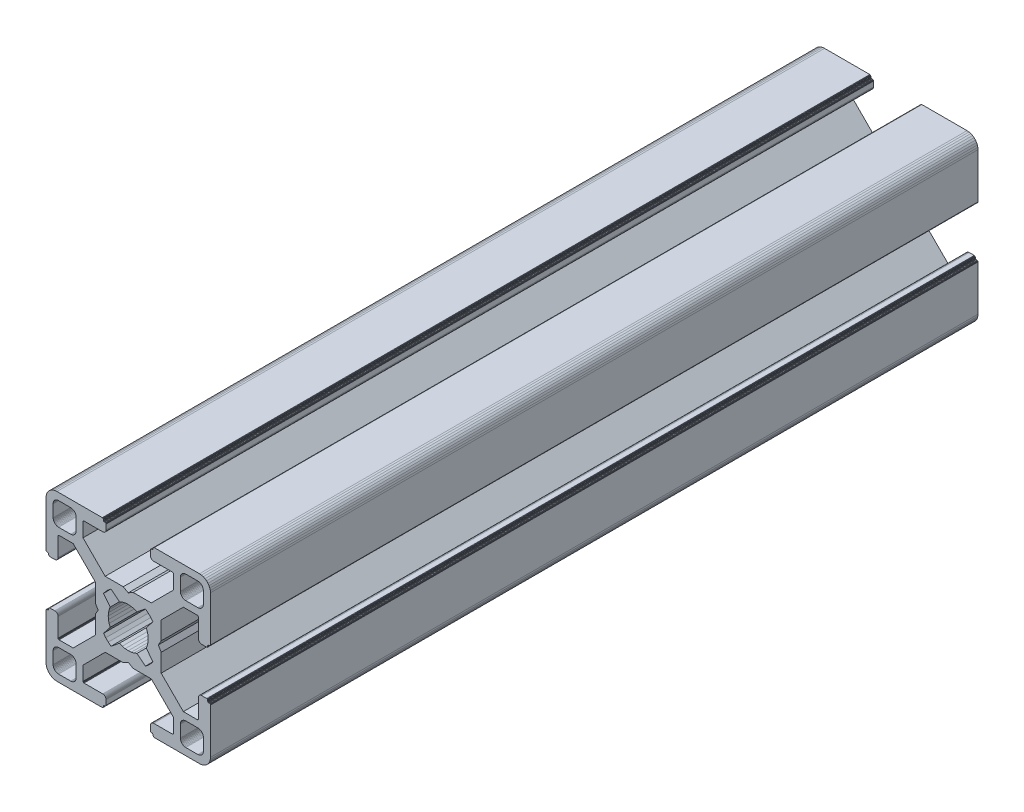
SolidWorks part; units mm, degrees
ref_plane "Front Plane" through (0, 0, 0) normal (0, 0, 1) x (1, 0, 0)
ref_plane "Top Plane" through (0, 0, 0) normal (0, 1, 0) x (1, 0, 0)
ref_plane "Right Plane" through (0, 0, 0) normal (1, 0, 0) x (0, 0, -1)
ref_plane "Plane1" through (0, 0, 0) normal (0, 0, 1) x (1, 0, 0)
sketch "Sketch1" plane through (0, 0, 0) normal (0, 0, 1) x (1, 0, 0)
  line L0 (28.3473, 29.9696) -> (28, 30)
  line L1 (28, 30) -> (19.75, 30)
  line L2 (19.75, 30) -> (19.7153, 29.997)
  line L3 (19.7153, 29.997) -> (19.6816, 29.9879)
  line L4 (19.6816, 29.9879) -> (19.65, 29.9732)
  line L5 (19.65, 29.9732) -> (19.6214, 29.9532)
  line L6 (19.6214, 29.9532) -> (19.5968, 29.9286)
  line L7 (19.5968, 29.9286) -> (19.5768, 29.9)
  line L8 (19.5768, 29.9) -> (19.5621, 29.8684)
  line L9 (19.5621, 29.8684) -> (19.553, 29.8347)
  line L10 (19.553, 29.8347) -> (19.55, 29.8)
  line L11 (19.55, 29.8) -> (19.55, 29.7)
  line L12 (19.55, 29.7) -> (19.547, 29.6653)
  line L13 (19.547, 29.6653) -> (19.5379, 29.6316)
  line L14 (19.5379, 29.6316) -> (19.5232, 29.6)
  line L15 (19.5232, 29.6) -> (19.5032, 29.5714)
  line L16 (19.5032, 29.5714) -> (19.4786, 29.5468)
  line L17 (19.4786, 29.5468) -> (19.45, 29.5268)
  line L18 (19.45, 29.5268) -> (19.4184, 29.5121)
  line L19 (19.4184, 29.5121) -> (19.3847, 29.503)
  line L20 (19.3847, 29.503) -> (19.35, 29.5)
  line L21 (19.35, 29.5) -> (19.25, 29.5)
  line L22 (19.25, 29.5) -> (19.2153, 29.497)
  line L23 (19.2153, 29.497) -> (19.1816, 29.4879)
  line L24 (19.1816, 29.4879) -> (19.15, 29.4732)
  line L25 (19.15, 29.4732) -> (19.1214, 29.4532)
  line L26 (19.1214, 29.4532) -> (19.0968, 29.4286)
  line L27 (19.0968, 29.4286) -> (19.0768, 29.4)
  line L28 (19.0768, 29.4) -> (19.0621, 29.3684)
  line L29 (19.0621, 29.3684) -> (19.053, 29.3347)
  line L30 (19.053, 29.3347) -> (19.05, 29.3)
  line L31 (19.05, 29.3) -> (19.05, 28.4)
  line L32 (19.05, 28.4) -> (19.0591, 28.2958)
  line L33 (19.0591, 28.2958) -> (19.0862, 28.1948)
  line L34 (19.0862, 28.1948) -> (19.1304, 28.1)
  line L35 (19.1304, 28.1) -> (19.1904, 28.0143)
  line L36 (19.1904, 28.0143) -> (19.2643, 27.9404)
  line L37 (19.2643, 27.9404) -> (19.35, 27.8804)
  line L38 (19.35, 27.8804) -> (19.4448, 27.8362)
  line L39 (19.4448, 27.8362) -> (19.5458, 27.8091)
  line L40 (19.5458, 27.8091) -> (19.65, 27.8)
  line L41 (19.65, 27.8) -> (23.05, 27.8)
  line L42 (23.05, 27.8) -> (23.0847, 27.7969)
  line L43 (23.0847, 27.7969) -> (23.1184, 27.7879)
  line L44 (23.1184, 27.7879) -> (23.15, 27.7732)
  line L45 (23.15, 27.7732) -> (23.1786, 27.7532)
  line L46 (23.1786, 27.7532) -> (23.2032, 27.7285)
  line L47 (23.2032, 27.7285) -> (23.2232, 27.7)
  line L48 (23.2232, 27.7) -> (23.2379, 27.6684)
  line L49 (23.2379, 27.6684) -> (23.247, 27.6347)
  line L50 (23.247, 27.6347) -> (23.25, 27.6)
  line L51 (23.25, 27.6) -> (23.25, 25.05)
  line L52 (23.25, 25.05) -> (19.2045, 21)
  line L53 (19.2045, 21) -> (15.9, 21)
  line L54 (15.9, 21) -> (15, 20.4848)
  line L55 (15, 20.4848) -> (14.1, 21)
  line L56 (14.1, 21) -> (10.7955, 21)
  line L57 (10.7955, 21) -> (7.9973, 23.8013)
  line L58 (7.9973, 23.8013) -> (6.75, 25.05)
  line L59 (6.75, 25.05) -> (6.75, 27.6)
  line L60 (6.75, 27.6) -> (6.753, 27.6347)
  line L61 (6.753, 27.6347) -> (6.7621, 27.6684)
  line L62 (6.7621, 27.6684) -> (6.7768, 27.7)
  line L63 (6.7768, 27.7) -> (6.7968, 27.7285)
  line L64 (6.7968, 27.7285) -> (6.8215, 27.7532)
  line L65 (6.8215, 27.7532) -> (6.85, 27.7732)
  line L66 (6.85, 27.7732) -> (6.8816, 27.7879)
  line L67 (6.8816, 27.7879) -> (6.9153, 27.7969)
  line L68 (6.9153, 27.7969) -> (6.95, 27.8)
  line L69 (6.95, 27.8) -> (10.35, 27.8)
  line L70 (10.35, 27.8) -> (10.4542, 27.8091)
  line L71 (10.4542, 27.8091) -> (10.5552, 27.8362)
  line L72 (10.5552, 27.8362) -> (10.65, 27.8804)
  line L73 (10.65, 27.8804) -> (10.7357, 27.9404)
  line L74 (10.7357, 27.9404) -> (10.8096, 28.0143)
  line L75 (10.8096, 28.0143) -> (10.8696, 28.1)
  line L76 (10.8696, 28.1) -> (10.9138, 28.1948)
  line L77 (10.9138, 28.1948) -> (10.9409, 28.2958)
  line L78 (10.9409, 28.2958) -> (10.95, 28.4)
  line L79 (10.95, 28.4) -> (10.95, 29.3)
  line L80 (10.95, 29.3) -> (10.947, 29.3347)
  line L81 (10.947, 29.3347) -> (10.938, 29.3684)
  line L82 (10.938, 29.3684) -> (10.9232, 29.4)
  line L83 (10.9232, 29.4) -> (10.9032, 29.4286)
  line L84 (10.9032, 29.4286) -> (10.8786, 29.4532)
  line L85 (10.8786, 29.4532) -> (10.85, 29.4732)
  line L86 (10.85, 29.4732) -> (10.8184, 29.4879)
  line L87 (10.8184, 29.4879) -> (10.7847, 29.497)
  line L88 (10.7847, 29.497) -> (10.75, 29.5)
  line L89 (10.75, 29.5) -> (10.65, 29.5)
  line L90 (10.65, 29.5) -> (10.6153, 29.503)
  line L91 (10.6153, 29.503) -> (10.5816, 29.5121)
  line L92 (10.5816, 29.5121) -> (10.55, 29.5268)
  line L93 (10.55, 29.5268) -> (10.5214, 29.5468)
  line L94 (10.5214, 29.5468) -> (10.4968, 29.5714)
  line L95 (10.4968, 29.5714) -> (10.4768, 29.6)
  line L96 (10.4768, 29.6) -> (10.4621, 29.6316)
  line L97 (10.4621, 29.6316) -> (10.453, 29.6653)
  line L98 (10.453, 29.6653) -> (10.45, 29.7)
  line L99 (10.45, 29.7) -> (10.45, 29.8)
  line L100 (10.45, 29.8) -> (10.447, 29.8347)
  line L101 (10.447, 29.8347) -> (10.4379, 29.8684)
  line L102 (10.4379, 29.8684) -> (10.4232, 29.9)
  line L103 (10.4232, 29.9) -> (10.4032, 29.9286)
  line L104 (10.4032, 29.9286) -> (10.3786, 29.9532)
  line L105 (10.3786, 29.9532) -> (10.35, 29.9732)
  line L106 (10.35, 29.9732) -> (10.3184, 29.9879)
  line L107 (10.3184, 29.9879) -> (10.2847, 29.997)
  line L108 (10.2847, 29.997) -> (10.25, 30)
  line L109 (10.25, 30) -> (2, 30)
  line L110 (2, 30) -> (1.6527, 29.9696)
  line L111 (1.6527, 29.9696) -> (1.316, 29.8794)
  line L112 (1.316, 29.8794) -> (1, 29.7321)
  line L113 (1, 29.7321) -> (0.7144, 29.5321)
  line L114 (0.7144, 29.5321) -> (0.4679, 29.2856)
  line L115 (0.4679, 29.2856) -> (0.2679, 29)
  line L116 (0.2679, 29) -> (0.1206, 28.684)
  line L117 (0.1206, 28.684) -> (0.0304, 28.3473)
  line L118 (0.0304, 28.3473) -> (0, 28)
  line L119 (0, 28) -> (0, 19.75)
  line L120 (0, 19.75) -> (0.003, 19.7153)
  line L121 (0.003, 19.7153) -> (0.0121, 19.6816)
  line L122 (0.0121, 19.6816) -> (0.0268, 19.65)
  line L123 (0.0268, 19.65) -> (0.0468, 19.6214)
  line L124 (0.0468, 19.6214) -> (0.0714, 19.5968)
  line L125 (0.0714, 19.5968) -> (0.1, 19.5768)
  line L126 (0.1, 19.5768) -> (0.1316, 19.5621)
  line L127 (0.1316, 19.5621) -> (0.1653, 19.553)
  line L128 (0.1653, 19.553) -> (0.2, 19.55)
  line L129 (0.2, 19.55) -> (0.3, 19.55)
  line L130 (0.3, 19.55) -> (0.3347, 19.547)
  line L131 (0.3347, 19.547) -> (0.3684, 19.5379)
  line L132 (0.3684, 19.5379) -> (0.4, 19.5232)
  line L133 (0.4, 19.5232) -> (0.4286, 19.5032)
  line L134 (0.4286, 19.5032) -> (0.4532, 19.4786)
  line L135 (0.4532, 19.4786) -> (0.4732, 19.45)
  line L136 (0.4732, 19.45) -> (0.4879, 19.4184)
  line L137 (0.4879, 19.4184) -> (0.497, 19.3847)
  line L138 (0.497, 19.3847) -> (0.5, 19.35)
  line L139 (0.5, 19.35) -> (0.5, 19.25)
  line L140 (0.5, 19.25) -> (0.503, 19.2153)
  line L141 (0.503, 19.2153) -> (0.5121, 19.1816)
  line L142 (0.5121, 19.1816) -> (0.5268, 19.15)
  line L143 (0.5268, 19.15) -> (0.5468, 19.1214)
  line L144 (0.5468, 19.1214) -> (0.5714, 19.0968)
  line L145 (0.5714, 19.0968) -> (0.6, 19.0768)
  line L146 (0.6, 19.0768) -> (0.6316, 19.0621)
  line L147 (0.6316, 19.0621) -> (0.6653, 19.053)
  line L148 (0.6653, 19.053) -> (0.7, 19.05)
  line L149 (0.7, 19.05) -> (1.6, 19.05)
  line L150 (1.6, 19.05) -> (1.7042, 19.0591)
  line L151 (1.7042, 19.0591) -> (1.8052, 19.0862)
  line L152 (1.8052, 19.0862) -> (1.9, 19.1304)
  line L153 (1.9, 19.1304) -> (1.9857, 19.1904)
  line L154 (1.9857, 19.1904) -> (2.0596, 19.2643)
  line L155 (2.0596, 19.2643) -> (2.1196, 19.35)
  line L156 (2.1196, 19.35) -> (2.1638, 19.4448)
  line L157 (2.1638, 19.4448) -> (2.1909, 19.5458)
  line L158 (2.1909, 19.5458) -> (2.2, 19.65)
  line L159 (2.2, 19.65) -> (2.2, 23.05)
  line L160 (2.2, 23.05) -> (2.203, 23.0847)
  line L161 (2.203, 23.0847) -> (2.2121, 23.1184)
  line L162 (2.2121, 23.1184) -> (2.2268, 23.15)
  line L163 (2.2268, 23.15) -> (2.2468, 23.1786)
  line L164 (2.2468, 23.1786) -> (2.2714, 23.2032)
  line L165 (2.2714, 23.2032) -> (2.3, 23.2232)
  line L166 (2.3, 23.2232) -> (2.3316, 23.2379)
  line L167 (2.3316, 23.2379) -> (2.3653, 23.247)
  line L168 (2.3653, 23.247) -> (2.4, 23.25)
  line L169 (2.4, 23.25) -> (4.95, 23.25)
  line L170 (4.95, 23.25) -> (7.9973, 20.2027)
  line L171 (7.9973, 20.2027) -> (8.9955, 19.2045)
  line L172 (8.9955, 19.2045) -> (8.9955, 15.9)
  line L173 (8.9955, 15.9) -> (9.5151, 15)
  line L174 (9.5151, 15) -> (8.9955, 14.1)
  line L175 (8.9955, 14.1) -> (8.9955, 10.7955)
  line L176 (8.9955, 10.7955) -> (4.95, 6.75)
  line L177 (4.95, 6.75) -> (2.4, 6.75)
  line L178 (2.4, 6.75) -> (2.3653, 6.753)
  line L179 (2.3653, 6.753) -> (2.3316, 6.7621)
  line L180 (2.3316, 6.7621) -> (2.3, 6.7768)
  line L181 (2.3, 6.7768) -> (2.2714, 6.7968)
  line L182 (2.2714, 6.7968) -> (2.2468, 6.8214)
  line L183 (2.2468, 6.8214) -> (2.2268, 6.85)
  line L184 (2.2268, 6.85) -> (2.2121, 6.8816)
  line L185 (2.2121, 6.8816) -> (2.203, 6.9153)
  line L186 (2.203, 6.9153) -> (2.2, 6.95)
  line L187 (2.2, 6.95) -> (2.2, 10.35)
  line L188 (2.2, 10.35) -> (2.1909, 10.4542)
  line L189 (2.1909, 10.4542) -> (2.1638, 10.5552)
  line L190 (2.1638, 10.5552) -> (2.1196, 10.65)
  line L191 (2.1196, 10.65) -> (2.0596, 10.7357)
  line L192 (2.0596, 10.7357) -> (1.9857, 10.8096)
  line L193 (1.9857, 10.8096) -> (1.9, 10.8696)
  line L194 (1.9, 10.8696) -> (1.8052, 10.9138)
  line L195 (1.8052, 10.9138) -> (1.7042, 10.9409)
  line L196 (1.7042, 10.9409) -> (1.6, 10.95)
  line L197 (1.6, 10.95) -> (0.7, 10.95)
  line L198 (0.7, 10.95) -> (0.6653, 10.9469)
  line L199 (0.6653, 10.9469) -> (0.6316, 10.9379)
  line L200 (0.6316, 10.9379) -> (0.6, 10.9232)
  line L201 (0.6, 10.9232) -> (0.5715, 10.9032)
  line L202 (0.5715, 10.9032) -> (0.5468, 10.8785)
  line L203 (0.5468, 10.8785) -> (0.5268, 10.85)
  line L204 (0.5268, 10.85) -> (0.5121, 10.8184)
  line L205 (0.5121, 10.8184) -> (0.503, 10.7847)
  line L206 (0.503, 10.7847) -> (0.5, 10.75)
  line L207 (0.5, 10.75) -> (0.5, 10.65)
  line L208 (0.5, 10.65) -> (0.497, 10.6153)
  line L209 (0.497, 10.6153) -> (0.4879, 10.5816)
  line L210 (0.4879, 10.5816) -> (0.4732, 10.55)
  line L211 (0.4732, 10.55) -> (0.4532, 10.5214)
  line L212 (0.4532, 10.5214) -> (0.4286, 10.4968)
  line L213 (0.4286, 10.4968) -> (0.4, 10.4768)
  line L214 (0.4, 10.4768) -> (0.3684, 10.4621)
  line L215 (0.3684, 10.4621) -> (0.3347, 10.453)
  line L216 (0.3347, 10.453) -> (0.3, 10.45)
  line L217 (0.3, 10.45) -> (0.2, 10.45)
  line L218 (0.2, 10.45) -> (0.1653, 10.447)
  line L219 (0.1653, 10.447) -> (0.1316, 10.4379)
  line L220 (0.1316, 10.4379) -> (0.1, 10.4232)
  line L221 (0.1, 10.4232) -> (0.0714, 10.4032)
  line L222 (0.0714, 10.4032) -> (0.0468, 10.3786)
  line L223 (0.0468, 10.3786) -> (0.0268, 10.35)
  line L224 (0.0268, 10.35) -> (0.0121, 10.3184)
  line L225 (0.0121, 10.3184) -> (0.003, 10.2847)
  line L226 (0.003, 10.2847) -> (0, 10.25)
  line L227 (0, 10.25) -> (0, 2)
  line L228 (0, 2) -> (0.0304, 1.6527)
  line L229 (0.0304, 1.6527) -> (0.1206, 1.316)
  line L230 (0.1206, 1.316) -> (0.2679, 1)
  line L231 (0.2679, 1) -> (0.4679, 0.7144)
  line L232 (0.4679, 0.7144) -> (0.7144, 0.4679)
  line L233 (0.7144, 0.4679) -> (1, 0.2679)
  line L234 (1, 0.2679) -> (1.316, 0.1206)
  line L235 (1.316, 0.1206) -> (1.6527, 0.0304)
  line L236 (1.6527, 0.0304) -> (2, 0)
  line L237 (2, 0) -> (10.25, 0)
  line L238 (10.25, 0) -> (10.2847, 0.003)
  line L239 (10.2847, 0.003) -> (10.3184, 0.0121)
  line L240 (10.3184, 0.0121) -> (10.35, 0.0268)
  line L241 (10.35, 0.0268) -> (10.3786, 0.0468)
  line L242 (10.3786, 0.0468) -> (10.4032, 0.0714)
  line L243 (10.4032, 0.0714) -> (10.4232, 0.1)
  line L244 (10.4232, 0.1) -> (10.4379, 0.1316)
  line L245 (10.4379, 0.1316) -> (10.447, 0.1653)
  line L246 (10.447, 0.1653) -> (10.45, 0.2)
  line L247 (10.45, 0.2) -> (10.45, 0.3)
  line L248 (10.45, 0.3) -> (10.453, 0.3347)
  line L249 (10.453, 0.3347) -> (10.4621, 0.3684)
  line L250 (10.4621, 0.3684) -> (10.4768, 0.4)
  line L251 (10.4768, 0.4) -> (10.4968, 0.4286)
  line L252 (10.4968, 0.4286) -> (10.5214, 0.4532)
  line L253 (10.5214, 0.4532) -> (10.55, 0.4732)
  line L254 (10.55, 0.4732) -> (10.5816, 0.4879)
  line L255 (10.5816, 0.4879) -> (10.6153, 0.497)
  line L256 (10.6153, 0.497) -> (10.65, 0.5)
  line L257 (10.65, 0.5) -> (10.75, 0.5)
  line L258 (10.75, 0.5) -> (10.7847, 0.503)
  line L259 (10.7847, 0.503) -> (10.8184, 0.5121)
  line L260 (10.8184, 0.5121) -> (10.85, 0.5268)
  line L261 (10.85, 0.5268) -> (10.8785, 0.5468)
  line L262 (10.8785, 0.5468) -> (10.9032, 0.5715)
  line L263 (10.9032, 0.5715) -> (10.9232, 0.6)
  line L264 (10.9232, 0.6) -> (10.9379, 0.6316)
  line L265 (10.9379, 0.6316) -> (10.9469, 0.6653)
  line L266 (10.9469, 0.6653) -> (10.95, 0.7)
  line L267 (10.95, 0.7) -> (10.95, 1.6)
  line L268 (10.95, 1.6) -> (10.9409, 1.7042)
  line L269 (10.9409, 1.7042) -> (10.9138, 1.8052)
  line L270 (10.9138, 1.8052) -> (10.8696, 1.9)
  line L271 (10.8696, 1.9) -> (10.8096, 1.9857)
  line L272 (10.8096, 1.9857) -> (10.7357, 2.0596)
  line L273 (10.7357, 2.0596) -> (10.65, 2.1196)
  line L274 (10.65, 2.1196) -> (10.5552, 2.1638)
  line L275 (10.5552, 2.1638) -> (10.4542, 2.1909)
  line L276 (10.4542, 2.1909) -> (10.35, 2.2)
  line L277 (10.35, 2.2) -> (6.95, 2.2)
  line L278 (6.95, 2.2) -> (6.9153, 2.203)
  line L279 (6.9153, 2.203) -> (6.8816, 2.212)
  line L280 (6.8816, 2.212) -> (6.85, 2.2268)
  line L281 (6.85, 2.2268) -> (6.8215, 2.2468)
  line L282 (6.8215, 2.2468) -> (6.7968, 2.2714)
  line L283 (6.7968, 2.2714) -> (6.7768, 2.3)
  line L284 (6.7768, 2.3) -> (6.7621, 2.3316)
  line L285 (6.7621, 2.3316) -> (6.753, 2.3653)
  line L286 (6.753, 2.3653) -> (6.75, 2.4)
  line L287 (6.75, 2.4) -> (6.75, 4.95)
  line L288 (6.75, 4.95) -> (9.7875, 7.9908)
  line L289 (9.7875, 7.9908) -> (10.7955, 9)
  line L290 (10.7955, 9) -> (14.1, 9)
  line L291 (14.1, 9) -> (15, 9.5151)
  line L292 (15, 9.5151) -> (15.9, 9)
  line L293 (15.9, 9) -> (19.2045, 9)
  line L294 (19.2045, 9) -> (20.2126, 7.9908)
  line L295 (20.2126, 7.9908) -> (23.25, 4.95)
  line L296 (23.25, 4.95) -> (23.25, 2.4)
  line L297 (23.25, 2.4) -> (23.247, 2.3653)
  line L298 (23.247, 2.3653) -> (23.2379, 2.3316)
  line L299 (23.2379, 2.3316) -> (23.2232, 2.3)
  line L300 (23.2232, 2.3) -> (23.2032, 2.2714)
  line L301 (23.2032, 2.2714) -> (23.1786, 2.2468)
  line L302 (23.1786, 2.2468) -> (23.15, 2.2268)
  line L303 (23.15, 2.2268) -> (23.1184, 2.212)
  line L304 (23.1184, 2.212) -> (23.0847, 2.203)
  line L305 (23.0847, 2.203) -> (23.05, 2.2)
  line L306 (23.05, 2.2) -> (19.65, 2.2)
  line L307 (19.65, 2.2) -> (19.5458, 2.1909)
  line L308 (19.5458, 2.1909) -> (19.4448, 2.1638)
  line L309 (19.4448, 2.1638) -> (19.35, 2.1196)
  line L310 (19.35, 2.1196) -> (19.2643, 2.0596)
  line L311 (19.2643, 2.0596) -> (19.1904, 1.9857)
  line L312 (19.1904, 1.9857) -> (19.1304, 1.9)
  line L313 (19.1304, 1.9) -> (19.0862, 1.8052)
  line L314 (19.0862, 1.8052) -> (19.0591, 1.7042)
  line L315 (19.0591, 1.7042) -> (19.05, 1.6)
  line L316 (19.05, 1.6) -> (19.05, 0.7)
  line L317 (19.05, 0.7) -> (19.053, 0.6653)
  line L318 (19.053, 0.6653) -> (19.0621, 0.6316)
  line L319 (19.0621, 0.6316) -> (19.0768, 0.6)
  line L320 (19.0768, 0.6) -> (19.0968, 0.5714)
  line L321 (19.0968, 0.5714) -> (19.1214, 0.5468)
  line L322 (19.1214, 0.5468) -> (19.15, 0.5268)
  line L323 (19.15, 0.5268) -> (19.1816, 0.5121)
  line L324 (19.1816, 0.5121) -> (19.2153, 0.503)
  line L325 (19.2153, 0.503) -> (19.25, 0.5)
  line L326 (19.25, 0.5) -> (19.35, 0.5)
  line L327 (19.35, 0.5) -> (19.3847, 0.497)
  line L328 (19.3847, 0.497) -> (19.4184, 0.4879)
  line L329 (19.4184, 0.4879) -> (19.45, 0.4732)
  line L330 (19.45, 0.4732) -> (19.4786, 0.4532)
  line L331 (19.4786, 0.4532) -> (19.5032, 0.4286)
  line L332 (19.5032, 0.4286) -> (19.5232, 0.4)
  line L333 (19.5232, 0.4) -> (19.5379, 0.3684)
  line L334 (19.5379, 0.3684) -> (19.547, 0.3347)
  line L335 (19.547, 0.3347) -> (19.55, 0.3)
  line L336 (19.55, 0.3) -> (19.55, 0.2)
  line L337 (19.55, 0.2) -> (19.553, 0.1653)
  line L338 (19.553, 0.1653) -> (19.5621, 0.1316)
  line L339 (19.5621, 0.1316) -> (19.5768, 0.1)
  line L340 (19.5768, 0.1) -> (19.5968, 0.0714)
  line L341 (19.5968, 0.0714) -> (19.6214, 0.0468)
  line L342 (19.6214, 0.0468) -> (19.65, 0.0268)
  line L343 (19.65, 0.0268) -> (19.6816, 0.0121)
  line L344 (19.6816, 0.0121) -> (19.7153, 0.003)
  line L345 (19.7153, 0.003) -> (19.75, 0)
  line L346 (19.75, 0) -> (28, 0)
  line L347 (28, 0) -> (28.3473, 0.0304)
  line L348 (28.3473, 0.0304) -> (28.684, 0.1206)
  line L349 (28.684, 0.1206) -> (29, 0.2679)
  line L350 (29, 0.2679) -> (29.2856, 0.4679)
  line L351 (29.2856, 0.4679) -> (29.5321, 0.7144)
  line L352 (29.5321, 0.7144) -> (29.7321, 1)
  line L353 (29.7321, 1) -> (29.8794, 1.316)
  line L354 (29.8794, 1.316) -> (29.9696, 1.6527)
  line L355 (29.9696, 1.6527) -> (30, 2)
  line L356 (30, 2) -> (30, 10.25)
  line L357 (30, 10.25) -> (29.997, 10.2847)
  line L358 (29.997, 10.2847) -> (29.988, 10.3184)
  line L359 (29.988, 10.3184) -> (29.9732, 10.35)
  line L360 (29.9732, 10.35) -> (29.9532, 10.3785)
  line L361 (29.9532, 10.3785) -> (29.9286, 10.4032)
  line L362 (29.9286, 10.4032) -> (29.9, 10.4232)
  line L363 (29.9, 10.4232) -> (29.8684, 10.4379)
  line L364 (29.8684, 10.4379) -> (29.8347, 10.447)
  line L365 (29.8347, 10.447) -> (29.8, 10.45)
  line L366 (29.8, 10.45) -> (29.7, 10.45)
  line L367 (29.7, 10.45) -> (29.6649, 10.4534)
  line L368 (29.6649, 10.4534) -> (29.6312, 10.4624)
  line L369 (29.6312, 10.4624) -> (29.5996, 10.4772)
  line L370 (29.5996, 10.4772) -> (29.5711, 10.4972)
  line L371 (29.5711, 10.4972) -> (29.5464, 10.5218)
  line L372 (29.5464, 10.5218) -> (29.5264, 10.5504)
  line L373 (29.5264, 10.5504) -> (29.5117, 10.582)
  line L374 (29.5117, 10.582) -> (29.5027, 10.6156)
  line L375 (29.5027, 10.6156) -> (29.4996, 10.6504)
  line L376 (29.4996, 10.6504) -> (29.4996, 10.7504)
  line L377 (29.4996, 10.7504) -> (29.497, 10.7847)
  line L378 (29.497, 10.7847) -> (29.4879, 10.8184)
  line L379 (29.4879, 10.8184) -> (29.4732, 10.85)
  line L380 (29.4732, 10.85) -> (29.4532, 10.8785)
  line L381 (29.4532, 10.8785) -> (29.4286, 10.9032)
  line L382 (29.4286, 10.9032) -> (29.4, 10.9232)
  line L383 (29.4, 10.9232) -> (29.3684, 10.9379)
  line L384 (29.3684, 10.9379) -> (29.3347, 10.9469)
  line L385 (29.3347, 10.9469) -> (29.3, 10.95)
  line L386 (29.3, 10.95) -> (28.4, 10.95)
  line L387 (28.4, 10.95) -> (28.2958, 10.9409)
  line L388 (28.2958, 10.9409) -> (28.1948, 10.9138)
  line L389 (28.1948, 10.9138) -> (28.1, 10.8696)
  line L390 (28.1, 10.8696) -> (28.0143, 10.8096)
  line L391 (28.0143, 10.8096) -> (27.9404, 10.7357)
  line L392 (27.9404, 10.7357) -> (27.8804, 10.65)
  line L393 (27.8804, 10.65) -> (27.8362, 10.5552)
  line L394 (27.8362, 10.5552) -> (27.8091, 10.4542)
  line L395 (27.8091, 10.4542) -> (27.8, 10.35)
  line L396 (27.8, 10.35) -> (27.8, 6.95)
  line L397 (27.8, 6.95) -> (27.797, 6.9153)
  line L398 (27.797, 6.9153) -> (27.7879, 6.8816)
  line L399 (27.7879, 6.8816) -> (27.7732, 6.85)
  line L400 (27.7732, 6.85) -> (27.7532, 6.8214)
  line L401 (27.7532, 6.8214) -> (27.7286, 6.7968)
  line L402 (27.7286, 6.7968) -> (27.7, 6.7768)
  line L403 (27.7, 6.7768) -> (27.6684, 6.7621)
  line L404 (27.6684, 6.7621) -> (27.6347, 6.753)
  line L405 (27.6347, 6.753) -> (27.6, 6.75)
  line L406 (27.6, 6.75) -> (25.05, 6.75)
  line L407 (25.05, 6.75) -> (23.8092, 7.9908)
  line L408 (23.8092, 7.9908) -> (21.0045, 10.7955)
  line L409 (21.0045, 10.7955) -> (21.0045, 14.1)
  line L410 (21.0045, 14.1) -> (20.4849, 15)
  line L411 (20.4849, 15) -> (21.0045, 15.9)
  line L412 (21.0045, 15.9) -> (21.0045, 19.2045)
  line L413 (21.0045, 19.2045) -> (25.05, 23.25)
  line L414 (25.05, 23.25) -> (27.6, 23.25)
  line L415 (27.6, 23.25) -> (27.6347, 23.247)
  line L416 (27.6347, 23.247) -> (27.6684, 23.2379)
  line L417 (27.6684, 23.2379) -> (27.7, 23.2232)
  line L418 (27.7, 23.2232) -> (27.7286, 23.2032)
  line L419 (27.7286, 23.2032) -> (27.7532, 23.1786)
  line L420 (27.7532, 23.1786) -> (27.7732, 23.15)
  line L421 (27.7732, 23.15) -> (27.7879, 23.1184)
  line L422 (27.7879, 23.1184) -> (27.797, 23.0847)
  line L423 (27.797, 23.0847) -> (27.8, 23.05)
  line L424 (27.8, 23.05) -> (27.8, 19.65)
  line L425 (27.8, 19.65) -> (27.8091, 19.5458)
  line L426 (27.8091, 19.5458) -> (27.8362, 19.4448)
  line L427 (27.8362, 19.4448) -> (27.8804, 19.35)
  line L428 (27.8804, 19.35) -> (27.9404, 19.2643)
  line L429 (27.9404, 19.2643) -> (28.0143, 19.1904)
  line L430 (28.0143, 19.1904) -> (28.1, 19.1304)
  line L431 (28.1, 19.1304) -> (28.1948, 19.0862)
  line L432 (28.1948, 19.0862) -> (28.2958, 19.0591)
  line L433 (28.2958, 19.0591) -> (28.4, 19.05)
  line L434 (28.4, 19.05) -> (29.3, 19.05)
  line L435 (29.3, 19.05) -> (29.3347, 19.053)
  line L436 (29.3347, 19.053) -> (29.3684, 19.0621)
  line L437 (29.3684, 19.0621) -> (29.4, 19.0768)
  line L438 (29.4, 19.0768) -> (29.4282, 19.0971)
  line L439 (29.4282, 19.0971) -> (29.4528, 19.1218)
  line L440 (29.4528, 19.1218) -> (29.4728, 19.1504)
  line L441 (29.4728, 19.1504) -> (29.4876, 19.182)
  line L442 (29.4876, 19.182) -> (29.4966, 19.2156)
  line L443 (29.4966, 19.2156) -> (29.4996, 19.2504)
  line L444 (29.4996, 19.2504) -> (29.4996, 19.3504)
  line L445 (29.4996, 19.3504) -> (29.5027, 19.3851)
  line L446 (29.5027, 19.3851) -> (29.5117, 19.4188)
  line L447 (29.5117, 19.4188) -> (29.5264, 19.4504)
  line L448 (29.5264, 19.4504) -> (29.5464, 19.4789)
  line L449 (29.5464, 19.4789) -> (29.5711, 19.5036)
  line L450 (29.5711, 19.5036) -> (29.5996, 19.5236)
  line L451 (29.5996, 19.5236) -> (29.6312, 19.5383)
  line L452 (29.6312, 19.5383) -> (29.6649, 19.5473)
  line L453 (29.6649, 19.5473) -> (29.7, 19.55)
  line L454 (29.7, 19.55) -> (29.8, 19.55)
  line L455 (29.8, 19.55) -> (29.8347, 19.553)
  line L456 (29.8347, 19.553) -> (29.8684, 19.5621)
  line L457 (29.8684, 19.5621) -> (29.9, 19.5768)
  line L458 (29.9, 19.5768) -> (29.9286, 19.5968)
  line L459 (29.9286, 19.5968) -> (29.9532, 19.6214)
  line L460 (29.9532, 19.6214) -> (29.9732, 19.65)
  line L461 (29.9732, 19.65) -> (29.9879, 19.6816)
  line L462 (29.9879, 19.6816) -> (29.997, 19.7153)
  line L463 (29.997, 19.7153) -> (30, 19.75)
  line L464 (30, 19.75) -> (30, 28)
  line L465 (30, 28) -> (29.9696, 28.3473)
  line L466 (29.9696, 28.3473) -> (29.8794, 28.684)
  line L467 (29.8794, 28.684) -> (29.7321, 29)
  line L468 (29.7321, 29) -> (29.5321, 29.2856)
  line L469 (29.5321, 29.2856) -> (29.2856, 29.5321)
  line L470 (29.2856, 29.5321) -> (29, 29.7321)
  line L471 (29, 29.7321) -> (28.684, 29.8794)
  line L472 (28.684, 29.8794) -> (28.3473, 29.9696)
  line L473 (1.3, 25.5) -> (1.3, 27.7)
  line L474 (1.3, 27.7) -> (1.3123, 27.8564)
  line L475 (1.3123, 27.8564) -> (1.3489, 28.009)
  line L476 (1.3489, 28.009) -> (1.409, 28.154)
  line L477 (1.409, 28.154) -> (1.491, 28.2878)
  line L478 (1.491, 28.2878) -> (1.5929, 28.4071)
  line L479 (1.5929, 28.4071) -> (1.7122, 28.509)
  line L480 (1.7122, 28.509) -> (1.846, 28.591)
  line L481 (1.846, 28.591) -> (1.991, 28.6511)
  line L482 (1.991, 28.6511) -> (2.1436, 28.6877)
  line L483 (2.1436, 28.6877) -> (2.3, 28.7)
  line L484 (2.3, 28.7) -> (4.5, 28.7)
  line L485 (4.5, 28.7) -> (4.6564, 28.6877)
  line L486 (4.6564, 28.6877) -> (4.809, 28.6511)
  line L487 (4.809, 28.6511) -> (4.954, 28.591)
  line L488 (4.954, 28.591) -> (5.0878, 28.509)
  line L489 (5.0878, 28.509) -> (5.2071, 28.4071)
  line L490 (5.2071, 28.4071) -> (5.309, 28.2878)
  line L491 (5.309, 28.2878) -> (5.391, 28.154)
  line L492 (5.391, 28.154) -> (5.4511, 28.009)
  line L493 (5.4511, 28.009) -> (5.4877, 27.8564)
  line L494 (5.4877, 27.8564) -> (5.5, 27.7)
  line L495 (5.5, 27.7) -> (5.5, 25.5)
  line L496 (5.5, 25.5) -> (5.4877, 25.3436)
  line L497 (5.4877, 25.3436) -> (5.4511, 25.191)
  line L498 (5.4511, 25.191) -> (5.391, 25.046)
  line L499 (5.391, 25.046) -> (5.309, 24.9122)
  line L500 (5.309, 24.9122) -> (5.2071, 24.7929)
  line L501 (5.2071, 24.7929) -> (5.0878, 24.691)
  line L502 (5.0878, 24.691) -> (4.954, 24.609)
  line L503 (4.954, 24.609) -> (4.809, 24.5489)
  line L504 (4.809, 24.5489) -> (4.6564, 24.5123)
  line L505 (4.6564, 24.5123) -> (4.5, 24.5)
  line L506 (4.5, 24.5) -> (2.3, 24.5)
  line L507 (2.3, 24.5) -> (2.1436, 24.5123)
  line L508 (2.1436, 24.5123) -> (1.991, 24.5489)
  line L509 (1.991, 24.5489) -> (1.846, 24.609)
  line L510 (1.846, 24.609) -> (1.7122, 24.691)
  line L511 (1.7122, 24.691) -> (1.5929, 24.7929)
  line L512 (1.5929, 24.7929) -> (1.491, 24.9122)
  line L513 (1.491, 24.9122) -> (1.409, 25.046)
  line L514 (1.409, 25.046) -> (1.3489, 25.191)
  line L515 (1.3489, 25.191) -> (1.3123, 25.3436)
  line L516 (1.3123, 25.3436) -> (1.3, 25.5)
  line L517 (25.3436, 28.6877) -> (25.5, 28.7)
  line L518 (25.5, 28.7) -> (27.7, 28.7)
  line L519 (27.7, 28.7) -> (27.8564, 28.6877)
  line L520 (27.8564, 28.6877) -> (28.009, 28.6511)
  line L521 (28.009, 28.6511) -> (28.154, 28.591)
  line L522 (28.154, 28.591) -> (28.2878, 28.509)
  line L523 (28.2878, 28.509) -> (28.4071, 28.4071)
  line L524 (28.4071, 28.4071) -> (28.509, 28.2878)
  line L525 (28.509, 28.2878) -> (28.591, 28.154)
  line L526 (28.591, 28.154) -> (28.6511, 28.009)
  line L527 (28.6511, 28.009) -> (28.6877, 27.8564)
  line L528 (28.6877, 27.8564) -> (28.7, 27.7)
  line L529 (28.7, 27.7) -> (28.7, 25.5)
  line L530 (28.7, 25.5) -> (28.6877, 25.3436)
  line L531 (28.6877, 25.3436) -> (28.6511, 25.191)
  line L532 (28.6511, 25.191) -> (28.591, 25.046)
  line L533 (28.591, 25.046) -> (28.509, 24.9122)
  line L534 (28.509, 24.9122) -> (28.4071, 24.7929)
  line L535 (28.4071, 24.7929) -> (28.2878, 24.691)
  line L536 (28.2878, 24.691) -> (28.154, 24.609)
  line L537 (28.154, 24.609) -> (28.009, 24.5489)
  line L538 (28.009, 24.5489) -> (27.8564, 24.5123)
  line L539 (27.8564, 24.5123) -> (27.7, 24.5)
  line L540 (27.7, 24.5) -> (25.5, 24.5)
  line L541 (25.5, 24.5) -> (25.3436, 24.5123)
  line L542 (25.3436, 24.5123) -> (25.191, 24.5489)
  line L543 (25.191, 24.5489) -> (25.046, 24.609)
  line L544 (25.046, 24.609) -> (24.9122, 24.691)
  line L545 (24.9122, 24.691) -> (24.7929, 24.7929)
  line L546 (24.7929, 24.7929) -> (24.691, 24.9122)
  line L547 (24.691, 24.9122) -> (24.609, 25.046)
  line L548 (24.609, 25.046) -> (24.5489, 25.191)
  line L549 (24.5489, 25.191) -> (24.5123, 25.3436)
  line L550 (24.5123, 25.3436) -> (24.5, 25.5)
  line L551 (24.5, 25.5) -> (24.5, 27.7)
  line L552 (24.5, 27.7) -> (24.5123, 27.8564)
  line L553 (24.5123, 27.8564) -> (24.5489, 28.009)
  line L554 (24.5489, 28.009) -> (24.609, 28.154)
  line L555 (24.609, 28.154) -> (24.691, 28.2878)
  line L556 (24.691, 28.2878) -> (24.7929, 28.4071)
  line L557 (24.7929, 28.4071) -> (24.9122, 28.509)
  line L558 (24.9122, 28.509) -> (25.046, 28.591)
  line L559 (25.046, 28.591) -> (25.191, 28.6511)
  line L560 (25.191, 28.6511) -> (25.3436, 28.6877)
  line L561 (15, 18.65) -> (15.55, 18.6083)
  line L562 (15.55, 18.6083) -> (16.0875, 18.4842)
  line L563 (16.0875, 18.4842) -> (16.6001, 18.2806)
  line L564 (16.6001, 18.2806) -> (18.1359, 19.5184)
  line L565 (18.1359, 19.5184) -> (18.645, 19.1187)
  line L566 (18.645, 19.1187) -> (19.1036, 18.6621)
  line L567 (19.1036, 18.6621) -> (19.5053, 18.1547)
  line L568 (19.5053, 18.1547) -> (18.2806, 16.6001)
  line L569 (18.2806, 16.6001) -> (18.4842, 16.0875)
  line L570 (18.4842, 16.0875) -> (18.6083, 15.55)
  line L571 (18.6083, 15.55) -> (18.65, 15)
  line L572 (18.65, 15) -> (18.6083, 14.45)
  line L573 (18.6083, 14.45) -> (18.4842, 13.9125)
  line L574 (18.4842, 13.9125) -> (18.2806, 13.3999)
  line L575 (18.2806, 13.3999) -> (19.5053, 11.8453)
  line L576 (19.5053, 11.8453) -> (19.1036, 11.3379)
  line L577 (19.1036, 11.3379) -> (18.645, 10.8813)
  line L578 (18.645, 10.8813) -> (18.1359, 10.4816)
  line L579 (18.1359, 10.4816) -> (16.6001, 11.7194)
  line L580 (16.6001, 11.7194) -> (16.0875, 11.5158)
  line L581 (16.0875, 11.5158) -> (15.55, 11.3917)
  line L582 (15.55, 11.3917) -> (15, 11.35)
  line L583 (15, 11.35) -> (14.45, 11.3917)
  line L584 (14.45, 11.3917) -> (13.9125, 11.5158)
  line L585 (13.9125, 11.5158) -> (13.3999, 11.7194)
  line L586 (13.3999, 11.7194) -> (11.8641, 10.4816)
  line L587 (11.8641, 10.4816) -> (11.355, 10.8813)
  line L588 (11.355, 10.8813) -> (10.8964, 11.3379)
  line L589 (10.8964, 11.3379) -> (10.4947, 11.8453)
  line L590 (10.4947, 11.8453) -> (11.7194, 13.3999)
  line L591 (11.7194, 13.3999) -> (11.5158, 13.9125)
  line L592 (11.5158, 13.9125) -> (11.3917, 14.45)
  line L593 (11.3917, 14.45) -> (11.35, 15)
  line L594 (11.35, 15) -> (11.3917, 15.55)
  line L595 (11.3917, 15.55) -> (11.5158, 16.0875)
  line L596 (11.5158, 16.0875) -> (11.7194, 16.6001)
  line L597 (11.7194, 16.6001) -> (10.4947, 18.1547)
  line L598 (10.4947, 18.1547) -> (10.8964, 18.6621)
  line L599 (10.8964, 18.6621) -> (11.355, 19.1187)
  line L600 (11.355, 19.1187) -> (11.8641, 19.5184)
  line L601 (11.8641, 19.5184) -> (13.3999, 18.2806)
  line L602 (13.3999, 18.2806) -> (13.9125, 18.4842)
  line L603 (13.9125, 18.4842) -> (14.45, 18.6083)
  line L604 (14.45, 18.6083) -> (15, 18.65)
  line L605 (4.5, 1.3) -> (2.3, 1.3)
  line L606 (2.3, 1.3) -> (2.1436, 1.3123)
  line L607 (2.1436, 1.3123) -> (1.991, 1.3489)
  line L608 (1.991, 1.3489) -> (1.846, 1.409)
  line L609 (1.846, 1.409) -> (1.7122, 1.491)
  line L610 (1.7122, 1.491) -> (1.5929, 1.5929)
  line L611 (1.5929, 1.5929) -> (1.491, 1.7122)
  line L612 (1.491, 1.7122) -> (1.409, 1.846)
  line L613 (1.409, 1.846) -> (1.3489, 1.991)
  line L614 (1.3489, 1.991) -> (1.3123, 2.1436)
  line L615 (1.3123, 2.1436) -> (1.3, 2.3)
  line L616 (1.3, 2.3) -> (1.3, 4.5)
  line L617 (1.3, 4.5) -> (1.3123, 4.6564)
  line L618 (1.3123, 4.6564) -> (1.3489, 4.809)
  line L619 (1.3489, 4.809) -> (1.409, 4.954)
  line L620 (1.409, 4.954) -> (1.491, 5.0878)
  line L621 (1.491, 5.0878) -> (1.5929, 5.2071)
  line L622 (1.5929, 5.2071) -> (1.7122, 5.309)
  line L623 (1.7122, 5.309) -> (1.846, 5.391)
  line L624 (1.846, 5.391) -> (1.991, 5.4511)
  line L625 (1.991, 5.4511) -> (2.1436, 5.4877)
  line L626 (2.1436, 5.4877) -> (2.3, 5.5)
  line L627 (2.3, 5.5) -> (4.5, 5.5)
  line L628 (4.5, 5.5) -> (4.6564, 5.4877)
  line L629 (4.6564, 5.4877) -> (4.809, 5.4511)
  line L630 (4.809, 5.4511) -> (4.954, 5.391)
  line L631 (4.954, 5.391) -> (5.0878, 5.309)
  line L632 (5.0878, 5.309) -> (5.2071, 5.2071)
  line L633 (5.2071, 5.2071) -> (5.309, 5.0878)
  line L634 (5.309, 5.0878) -> (5.391, 4.954)
  line L635 (5.391, 4.954) -> (5.4511, 4.809)
  line L636 (5.4511, 4.809) -> (5.4877, 4.6564)
  line L637 (5.4877, 4.6564) -> (5.5, 4.5)
  line L638 (5.5, 4.5) -> (5.5, 2.3)
  line L639 (5.5, 2.3) -> (5.4877, 2.1436)
  line L640 (5.4877, 2.1436) -> (5.4511, 1.991)
  line L641 (5.4511, 1.991) -> (5.391, 1.846)
  line L642 (5.391, 1.846) -> (5.309, 1.7122)
  line L643 (5.309, 1.7122) -> (5.2071, 1.5929)
  line L644 (5.2071, 1.5929) -> (5.0878, 1.491)
  line L645 (5.0878, 1.491) -> (4.954, 1.409)
  line L646 (4.954, 1.409) -> (4.809, 1.3489)
  line L647 (4.809, 1.3489) -> (4.6564, 1.3123)
  line L648 (4.6564, 1.3123) -> (4.5, 1.3)
  line L649 (27.7, 1.3) -> (25.5, 1.3)
  line L650 (25.5, 1.3) -> (25.3436, 1.3123)
  line L651 (25.3436, 1.3123) -> (25.191, 1.3489)
  line L652 (25.191, 1.3489) -> (25.046, 1.409)
  line L653 (25.046, 1.409) -> (24.9122, 1.491)
  line L654 (24.9122, 1.491) -> (24.7929, 1.5929)
  line L655 (24.7929, 1.5929) -> (24.691, 1.7122)
  line L656 (24.691, 1.7122) -> (24.609, 1.846)
  line L657 (24.609, 1.846) -> (24.5489, 1.991)
  line L658 (24.5489, 1.991) -> (24.5123, 2.1436)
  line L659 (24.5123, 2.1436) -> (24.5, 2.3)
  line L660 (24.5, 2.3) -> (24.5, 4.5)
  line L661 (24.5, 4.5) -> (24.5123, 4.6564)
  line L662 (24.5123, 4.6564) -> (24.5489, 4.809)
  line L663 (24.5489, 4.809) -> (24.609, 4.954)
  line L664 (24.609, 4.954) -> (24.691, 5.0878)
  line L665 (24.691, 5.0878) -> (24.7929, 5.2071)
  line L666 (24.7929, 5.2071) -> (24.9122, 5.309)
  line L667 (24.9122, 5.309) -> (25.046, 5.391)
  line L668 (25.046, 5.391) -> (25.191, 5.4511)
  line L669 (25.191, 5.4511) -> (25.3436, 5.4877)
  line L670 (25.3436, 5.4877) -> (25.5, 5.5)
  line L671 (25.5, 5.5) -> (27.7, 5.5)
  line L672 (27.7, 5.5) -> (27.8564, 5.4877)
  line L673 (27.8564, 5.4877) -> (28.009, 5.4511)
  line L674 (28.009, 5.4511) -> (28.154, 5.391)
  line L675 (28.154, 5.391) -> (28.2878, 5.309)
  line L676 (28.2878, 5.309) -> (28.4071, 5.2071)
  line L677 (28.4071, 5.2071) -> (28.509, 5.0878)
  line L678 (28.509, 5.0878) -> (28.591, 4.954)
  line L679 (28.591, 4.954) -> (28.6511, 4.809)
  line L680 (28.6511, 4.809) -> (28.6877, 4.6564)
  line L681 (28.6877, 4.6564) -> (28.7, 4.5)
  line L682 (28.7, 4.5) -> (28.7, 2.3)
  line L683 (28.7, 2.3) -> (28.6877, 2.1436)
  line L684 (28.6877, 2.1436) -> (28.6511, 1.991)
  line L685 (28.6511, 1.991) -> (28.591, 1.846)
  line L686 (28.591, 1.846) -> (28.509, 1.7122)
  line L687 (28.509, 1.7122) -> (28.4071, 1.5929)
  line L688 (28.4071, 1.5929) -> (28.2878, 1.491)
  line L689 (28.2878, 1.491) -> (28.154, 1.409)
  line L690 (28.154, 1.409) -> (28.009, 1.3489)
  line L691 (28.009, 1.3489) -> (27.8564, 1.3123)
  line L692 (27.8564, 1.3123) -> (27.7, 1.3)
extrude "Boss-Extrude1" add sketch "Sketch1" against normal blind 140
